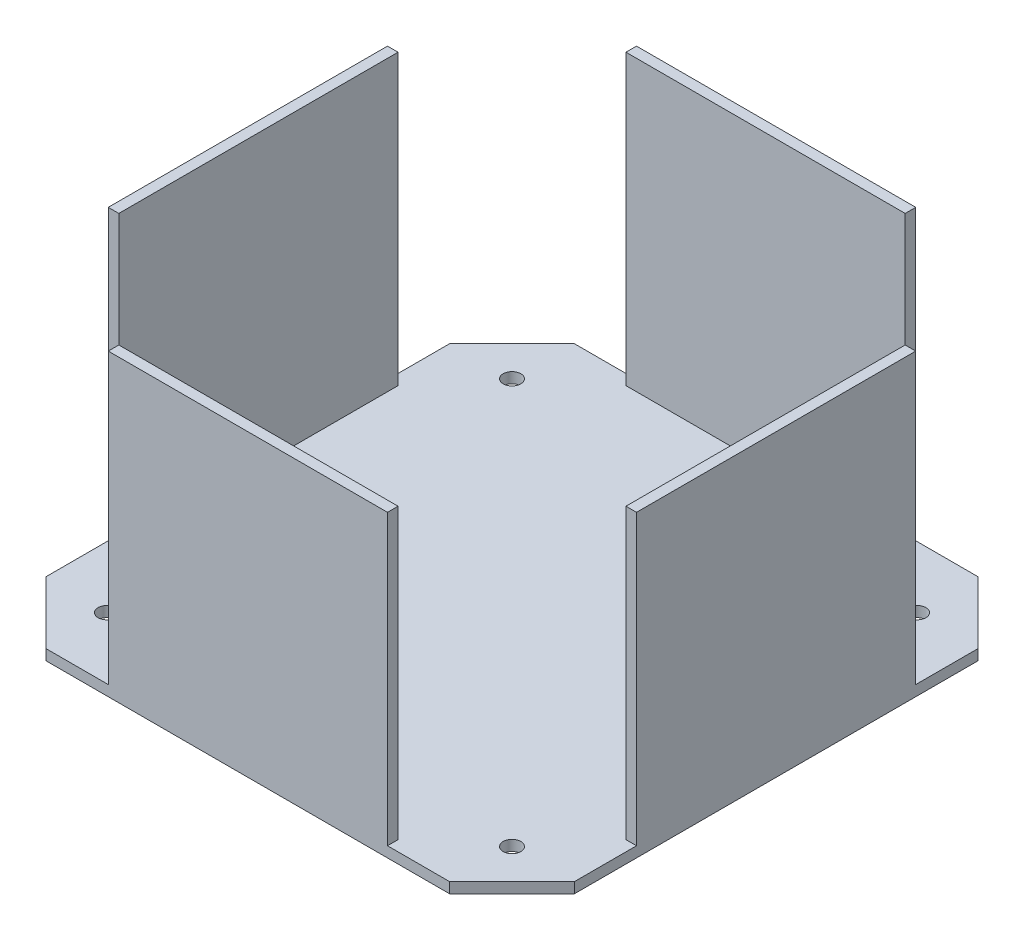
SolidWorks part; units mm, degrees
ref_plane "Front Plane" through (0, 0, 0) normal (0, 0, 1) x (1, 0, 0)
ref_plane "Top Plane" through (0, 0, 0) normal (0, 1, 0) x (1, 0, 0)
ref_plane "Right Plane" through (0, 0, 0) normal (1, 0, 0) x (0, 0, -1)
sketch "Sketch2" plane through (0, 0, 0) normal (0, 1, 0) x (1, 0, 0)
  line L1 (75, -75) -> (-75, -75)
  line L2 (75, -75) -> (75, 75)
  line L3 (75, 75) -> (-75, 75)
  line L4 (-75, -75) -> (-75, 75)
  line L5 (75, -75) -> (-75, 75) construction
  line L6 (75, 75) -> (-75, -75) construction
  point P0 (0, 0)
  dimension "D1" = 150
  dimension "D2" = 150
extrude "Boss-Extrude1" add sketch "Sketch2" along normal blind 85
shell "Shell1" thickness 3
sketch "Sketch3" plane through (0, 85, 0) normal (0, 1, 0) x (1, 0, 0)
  line L0 (39.6447, -75) -> (75, -39.6447) construction
  line L1 (-75, -75) -> (75, -75) construction
  line L2 (75, -75) -> (75, 75) construction
  line L3 (39.6447, -75) -> (75, -75)
  line L4 (75, -75) -> (75, -39.6447)
  line L5 (39.6447, -75) -> (39.6447, -72)
  line L6 (-72, -72) -> (72, -72) construction
  line L8 (-39.6447, -72) -> (-42.6447, -72)
  line L9 (75, -39.6447) -> (72, -39.6447)
  line L10 (72, -72) -> (72, 72) construction
  line L11 (72, -39.6447) -> (72, -42.6447)
  line L13 (72, -42.6447) -> (72, -72)
  line L14 (72, -72) -> (39.6447, -72)
  line L15 (-39.6447, -75) -> (-39.6447, -72)
  line L16 (-75, -75) -> (-39.6447, -75)
  line L17 (-75, -39.6447) -> (-75, -75)
  line L18 (-75, -39.6447) -> (-72, -39.6447)
  line L19 (-72, -72) -> (-72, -39.6447)
  line L20 (-42.6447, -72) -> (-72, -72)
  line L21 (-72, 39.6447) -> (-72, 42.6447)
  line L22 (-75, 39.6447) -> (-72, 39.6447)
  line L23 (-75, 75) -> (-75, 39.6447)
  line L24 (-39.6447, 75) -> (-75, 75)
  line L25 (-39.6447, 75) -> (-39.6447, 72)
  line L26 (-72, 72) -> (-39.6447, 72)
  line L27 (-72, 42.6447) -> (-72, 72)
  line L28 (39.6447, 72) -> (42.6447, 72)
  line L29 (39.6447, 75) -> (39.6447, 72)
  line L30 (75, 75) -> (39.6447, 75)
  line L31 (75, 39.6447) -> (75, 75)
  line L32 (75, 39.6447) -> (72, 39.6447)
  line L34 (42.6447, 72) -> (72, 72)
  line L35 (72, 72) -> (72, 39.6447)
  line L36 (72, 72) -> (72, 39.6447)
  point P41 (0, 0)
  dimension "D1" = 50
  dimension "D2" = 45
  dimension "D3" = 4
extrude "Cut-Extrude1" cut sketch "Sketch3" against normal up to surface (82 mm away) up to face at (0, 3, 0)
sketch "Sketch4" plane through (0, 3, 0) normal (0, 1, 0) x (1, 0, 0)
  line L0 (-75, -57.3223) -> (-75, -75)
  line L1 (-75, -75) -> (-75, -39.6447) construction
  line L2 (-75, -75) -> (-57.3223, -75)
  line L3 (-39.6447, -75) -> (-75, -75) construction
  line L4 (-57.3223, -75) -> (-75, -57.3223)
  line L5 (-75, 57.3223) -> (-57.3223, 75)
  line L6 (-57.3223, 75) -> (-75, 75)
  line L7 (-75, 75) -> (-75, 57.3223)
  line L8 (57.3223, 75) -> (75, 57.3223)
  line L9 (75, 57.3223) -> (75, 75)
  line L10 (75, 75) -> (57.3223, 75)
  line L11 (75, -57.3223) -> (57.3223, -75)
  line L12 (57.3223, -75) -> (75, -75)
  line L13 (75, -75) -> (75, -57.3223)
  point P20 (0, 0)
  dimension "D1" = 4
extrude "Cut-Extrude2" cut sketch "Sketch4" against normal through all
sketch "Sketch5" plane through (0, 3, 0) normal (0, 1, 0) x (1, 0, 0)
  line L0 (75, 57.3223) -> (75, 39.6447) construction
  circle A0 centre (57.5115, 57.5115) radius 2.5
  circle A1 centre (57.5115, -57.5115) radius 2.5
  circle A2 centre (-57.5115, -57.5115) radius 2.5
  circle A3 centre (-57.5115, 57.5115) radius 2.5
  point P15 (0, 0)
  dimension "D1" = 5
  dimension "D2" = 17.4885
  dimension "D3" = 17.4885
  dimension "D4" = 4
extrude "Cut-Extrude3" cut sketch "Sketch5" against normal through all
